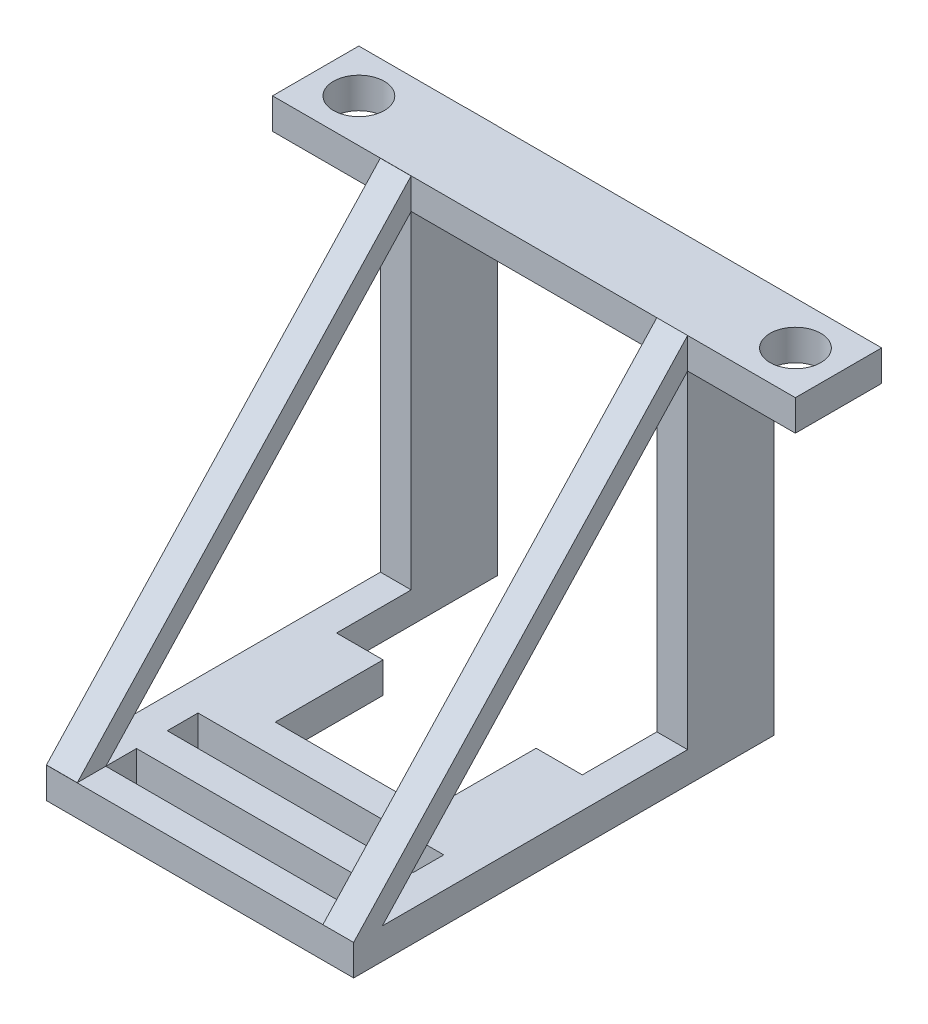
SolidWorks part; units mm, degrees
ref_plane "Front Plane" through (0, 0, 0) normal (0, 0, 1) x (1, 0, 0)
ref_plane "Top Plane" through (0, 0, 0) normal (0, 1, 0) x (1, 0, 0)
ref_plane "Right Plane" through (0, 0, 0) normal (1, 0, 0) x (0, 0, -1)
sketch "Sketch1" plane through (0, 0, 0) normal (0, 1, 0) x (1, 0, 0)
  line L0 (-34.5633, 0) -> (-20.3833, 0) construction
  line L1 (-35.9682, 1.4028) -> (-18.9863, 1.4028)
  line L2 (-18.9863, -1.3998) -> (-35.9682, -1.3998)
  line L6 (-18.9863, 1.4028) -> (-18.9863, -1.3998)
  line L9 (-35.9682, -1.3998) -> (-35.9682, 1.4028)
  circle A0 centre (-34.5633, 0) radius 0.825
  circle A1 centre (-20.3833, 0) radius 0.825
extrude "Boss-Extrude1" add sketch "Sketch1" along normal blind 1
sketch "Sketch2" plane through (-18.9863, 0, 0) normal (1, 0, 0) x (0, 0, -1)
  line L0 (-1.3998, 0) -> (-1.3998, -25.65) construction
  line L1 (-1.3998, -25.65) -> (-23.0935, -25.65) construction
  line L2 (-23.0935, -25.65) -> (-23.0935, -11.65) construction
  line L3 (-23.0935, -11.65) -> (-1.3998, -11.65) construction
sketch "Sketch3" plane through (0, 1, 0) normal (0, 1, 0) x (1, 0, 0)
  line L0 (-27.4773, 1.4028) -> (-27.4773, -1.3998) construction
  line L1 (-18.9863, 1.4028) -> (-35.9682, 1.4028) construction
  line L2 (-35.9682, -1.3998) -> (-18.9863, -1.3998) construction
  line L6 (-31.4809, -1.3998) -> (-23.4737, -1.3998)
  line L7 (-31.4809, -1.3998) -> (-31.4809, 1.4028)
  line L8 (-31.4809, 1.4028) -> (-23.4737, 1.4028)
  line L9 (-23.4737, -1.3998) -> (-23.4737, 1.4028)
sketch "Sketch5" plane through (-18.9863, 0, 0) normal (1, 0, 0) x (0, 0, -1)
  line L0 (1.4028, 1) -> (1.4028, -11.65)
  line L1 (-200023.0935, -11.65) -> (199998.6002, -11.65) construction
  line L2 (1.4028, -11.65) -> (-12.2467, -11.65)
  line L3 (-12.2467, -11.65) -> (-12.2467, -10.65)
  line L5 (-1.3998, 0) -> (-1.3998, -25.65) construction
  line L7 (-1.3998, 1) -> (1.4028, 1)
  line L8 (-1.3998, 1) -> (-12.2467, -10.65)
  line L9 (-1.3998, 0) -> (-11.3156, -10.65)
  line L10 (-1.3998, 0) -> (-1.3998, -10.65)
  line L11 (-11.3156, -10.65) -> (-1.3998, -10.65)
ref_plane "Plane3" through (-23.4863, 0, 0) normal (1, 0, 0) x (0, 0, -1)
ref_plane "Plane4" through (-31.4682, 0, 0) normal (-1, 0, 0) x (0, 0, 1)
sketch "Sketch9" plane through (-23.4863, 0, 0) normal (1, 0, 0) x (0, 0, -1)
  line L0 (1.4028, 1) -> (1.4028, -11.65)
  line L1 (1.4028, -11.65) -> (-12.2467, -11.65)
  line L2 (-12.2467, -11.65) -> (-12.2467, -10.65)
  line L3 (-1.3998, 1) -> (1.4028, 1)
  line L4 (-1.3998, 1) -> (-12.2467, -10.65)
  line L5 (-1.3998, 0) -> (-11.3156, -10.65)
  line L6 (-1.3998, 0) -> (-1.3998, -10.65)
  line L7 (-11.3156, -10.65) -> (-1.3998, -10.65)
extrude "Boss-Extrude4" add sketch "Sketch9" along normal blind 1
sketch "Sketch14" plane through (-31.4682, 0, 0) normal (-1, 0, 0) x (0, 0, 1)
  line L0 (-1.4069, 1) -> (-1.4069, -11.65)
  line L8 (11.3115, -10.65) -> (1.3957, -10.65)
  line L9 (1.3957, 0) -> (1.3957, -10.65)
  line L10 (1.3957, 0) -> (11.3115, -10.65)
  line L11 (1.3957, 1) -> (12.2426, -10.65)
  line L12 (1.3957, 1) -> (-1.4069, 1)
  line L13 (12.2426, -11.65) -> (12.2426, -10.65)
  line L14 (-1.4069, -11.65) -> (12.2426, -11.65)
extrude "Boss-Extrude5" add sketch "Sketch14" along normal blind 1
sketch "Sketch15" plane through (-22.4863, 0, 0) normal (1, 0, 0) x (0, 0, -1)
  line L0 (-200023.0935, -11.65) -> (199998.6002, -11.65) construction
  line L1 (-11.3156, -10.65) -> (-12.2467, -10.65)
  line L2 (-11.3156, -10.65) -> (-11.3156, -11.65)
  line L3 (-11.3156, -11.65) -> (-12.2467, -11.65)
  line L4 (-12.2467, -10.65) -> (-12.2467, -11.65)
  line L6 (-11.3156, -10.65) -> (-1.3998, -10.65) construction
  line L7 (-10.3171, -11.65) -> (-9.3182, -11.65)
  line L8 (-10.3171, -11.65) -> (-10.3171, -10.65)
  line L9 (-10.3171, -10.65) -> (-9.3182, -10.65)
  line L10 (-9.3182, -11.65) -> (-9.3182, -10.65)
  line L12 (-8.3193, -11.65) -> (-7.3203, -11.65)
  line L13 (-8.3193, -11.65) -> (-8.3193, -10.65)
  line L14 (-8.3193, -10.65) -> (-7.3203, -10.65)
  line L15 (-7.3203, -11.65) -> (-7.3203, -10.65)
extrude "Boss-Extrude6" add sketch "Sketch15" against normal up to surface (9.9819 mm away) up to face at (-32.4682, -4.3545, 3.097)
sketch "Sketch16" plane through (0, -11.65, 0) normal (0, -1, 0) x (1, 0, 0)
  line L1 (-23.4863, 7.3203) -> (-24.9863, 7.3203)
  line L2 (-23.4863, 7.3203) -> (-23.4863, 3.8203)
  line L3 (-23.4863, 3.8203) -> (-24.9863, 3.8203)
  line L4 (-24.9863, 7.3203) -> (-24.9863, 3.8203)
  line L5 (-31.4682, 7.3203) -> (-29.9582, 7.3203)
  line L6 (-31.4682, 7.3203) -> (-31.4682, 3.8203)
  line L7 (-31.4682, 3.8203) -> (-29.9582, 3.8203)
  line L8 (-29.9582, 7.3203) -> (-29.9582, 3.8203)
extrude "Boss-Extrude7" add sketch "Sketch16" against normal blind 1
